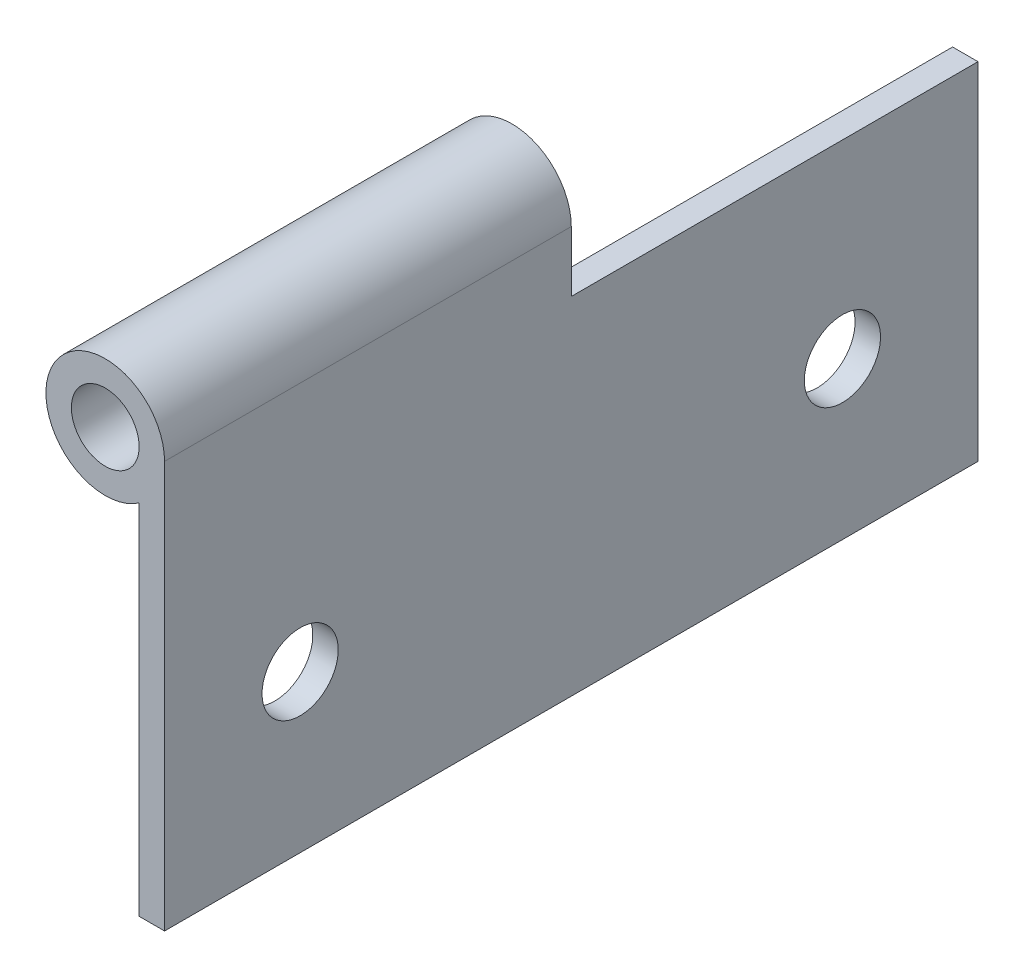
SolidWorks part; units mm, degrees
ref_plane "Front Plane" through (0, 0, 0) normal (0, 0, 1) x (1, 0, 0)
ref_plane "Top Plane" through (0, 0, 0) normal (0, 1, 0) x (1, 0, 0)
ref_plane "Right Plane" through (0, 0, 0) normal (1, 0, 0) x (0, 0, -1)
sketch "Sketch1" plane through (0, 0, 0) normal (0, 0, 1) x (1, 0, 0)
  line L0 (211.904, 88.8168) -> (214.5615, 88.8168) construction
  line L1 (214.2844, 56.4017) -> (214.2844, 94.5017)
  line L2 (211.904, 56.4017) -> (214.2844, 56.4017)
  line L3 (211.904, 56.4017) -> (211.904, 89.9425)
  circle A0 centre (208.3321, 95.0461) radius 6.2294 construction
  circle A1 centre (208.7282, 94.5017) radius 3.175
  arc A2 (214.2844, 94.5017) -> (211.904, 89.9425) centre (208.7282, 94.5017) ccw
extrude "Extrude1" add sketch "Sketch1" along normal blind 38.1
sketch "Sketch2" plane through (0, 0, 0) normal (0, 0, -1) x (-1, 0, 0)
  line L0 (-214.2844, 88.8294) -> (-214.2844, 56.4017)
  line L1 (-214.2844, 56.4017) -> (-214.2844, 94.5017) construction
  line L2 (-214.2844, 56.4017) -> (-211.904, 56.4017)
  line L3 (-211.904, 56.4017) -> (-211.904, 88.8294)
  line L4 (-211.904, 89.9425) -> (-211.904, 56.4017) construction
  line L5 (-211.904, 88.8294) -> (-214.2844, 88.8294)
extrude "Extrude2" add sketch "Sketch2" along normal blind 38.1
sketch "Sketch3" plane through (211.904, 0, 0) normal (-1, 0, 0) x (0, 0, 1)
  line L0 (0, 94.5017) -> (0, 71.0829) construction
  line L2 (0, 100.058) -> (0, 88.9455) construction
  line L3 (0, 71.0829) -> (-25.4, 71.0829) construction
  line L4 (0, 71.0829) -> (25.4, 71.0829) construction
  circle A0 centre (-25.4, 71.0829) radius 3.5687
  circle A1 centre (25.4, 71.0829) radius 3.5687
extrude "Cut-Extrude1" cut sketch "Sketch3" against normal up to surface (2.3804 mm away) up to face at (214.2844, 79.4383, -3.175)
